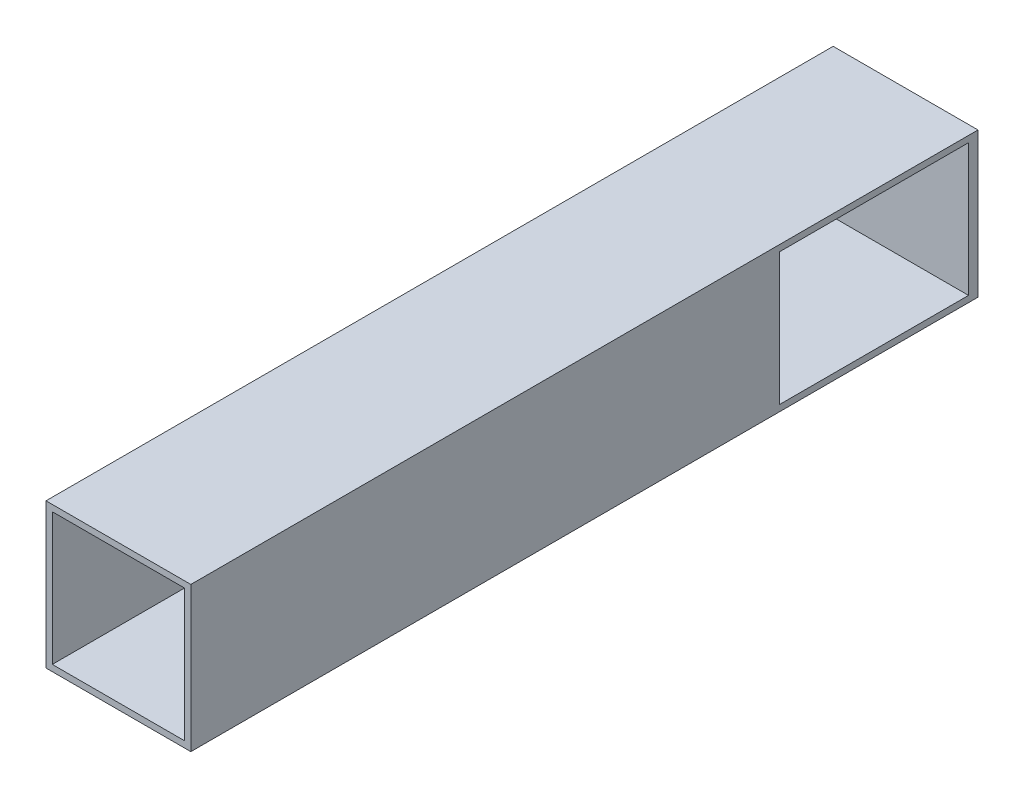
SolidWorks part; units mm, degrees
ref_plane "Front Plane" through (0, 0, 0) normal (0, 0, 1) x (1, 0, 0)
ref_plane "Top Plane" through (0, 0, 0) normal (0, 1, 0) x (1, 0, 0)
ref_plane "Right Plane" through (0, 0, 0) normal (1, 0, 0) x (0, 0, -1)
sketch "Sketch2" plane through (0, 0, 0) normal (0, 0, 1) x (1, 0, 0)
  line L1 (13.631, 15.2898) -> (130.471, 15.2898)
  line L2 (13.631, 15.2898) -> (13.631, -101.5502)
  line L3 (13.631, -101.5502) -> (130.471, -101.5502)
  line L4 (130.471, 15.2898) -> (130.471, -101.5502)
extrude "Boss-Extrude1" add sketch "Sketch2" along normal blind 635
sketch "Sketch3" plane through (0, 0, 635) normal (0, 0, 1) x (1, 0, 0)
  line L0 (18.711, 10.2098) -> (125.391, 10.2098)
  line L1 (125.391, -96.4702) -> (125.391, 10.2098)
  line L2 (18.711, -96.4702) -> (125.391, -96.4702)
  line L3 (18.711, -96.4702) -> (18.711, 10.2098)
  line L11 (21.251, -93.9302) -> (122.851, 7.6698) construction
  line L12 (21.251, 7.6698) -> (122.851, -93.9302) construction
  point P12 (72.051, -43.1302)
extrude "Cut-Extrude1" cut sketch "Sketch3" against normal blind 627.38
sketch "Sketch4" plane through (130.471, 0, 0) normal (1, 0, 0) x (0, 0, -1)
  line L0 (-7.62, -96.4702) -> (-160.02, -96.4702)
  line L3 (-160.02, 10.2098) -> (-7.62, 10.2098)
  line L8 (-160.02, -96.4702) -> (-160.02, 10.2098)
  line L9 (-7.62, -96.4702) -> (-7.62, 10.2098)
extrude "Cut-Extrude2" cut sketch "Sketch4" against normal blind 7.62
sketch "Sketch7" plane through (0, 0, 0) normal (1, 0, 0) x (0, 0, -1)
  line L0 (-635, -54.7067) -> (-629.92, -54.7067)
  line L1 (-635, -101.5502) -> (-635, 15.2898) construction
